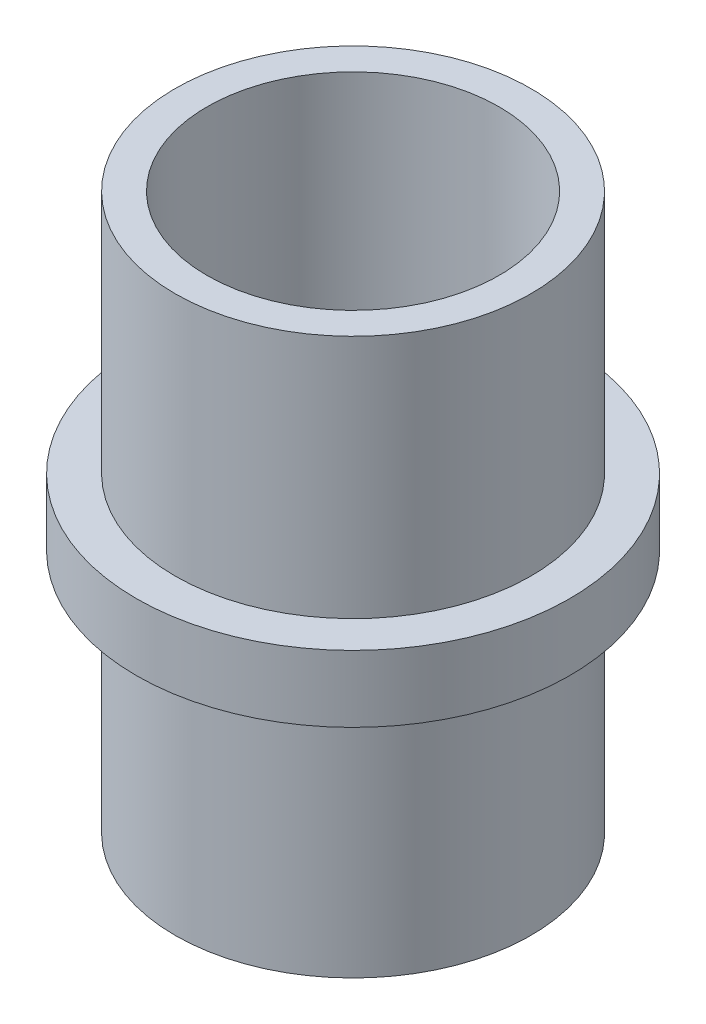
SolidWorks part; units mm, degrees
ref_plane "Front Plane" through (0, 0, 0) normal (0, 0, 1) x (1, 0, 0)
ref_plane "Top Plane" through (0, 0, 0) normal (0, 1, 0) x (1, 0, 0)
ref_plane "Right Plane" through (0, 0, 0) normal (1, 0, 0) x (0, 0, -1)
sketch "Sketch1" plane through (0, 0, 0) normal (0, 1, 0) x (1, 0, 0)
  circle A0 centre (0, 0) radius 13.1445
  circle A1 centre (0, 0) radius 16
  dimension "D1" = 26.289
  dimension "D2" = 32
extrude "Boss-Extrude1" add sketch "Sketch1" along normal mid plane 50
sketch "Sketch2" plane through (0, 0, 0) normal (0, 1, 0) x (1, 0, 0)
  circle A0 centre (0, 0) radius 16 construction
  circle A1 centre (0, 0) radius 16
  circle A2 centre (0, 0) radius 19.5
  dimension "D1" = 39
extrude "Boss-Extrude2" add sketch "Sketch2" along normal mid plane 6
sketch "Sketch3" plane through (0, 0, 0) normal (0, 0, 1) x (1, 0, 0)
  circle A0 centre (0, 0) radius 2
  dimension "D1" = 4
extrude "Cut-Extrude1" cut sketch "Sketch3" against normal up to next
